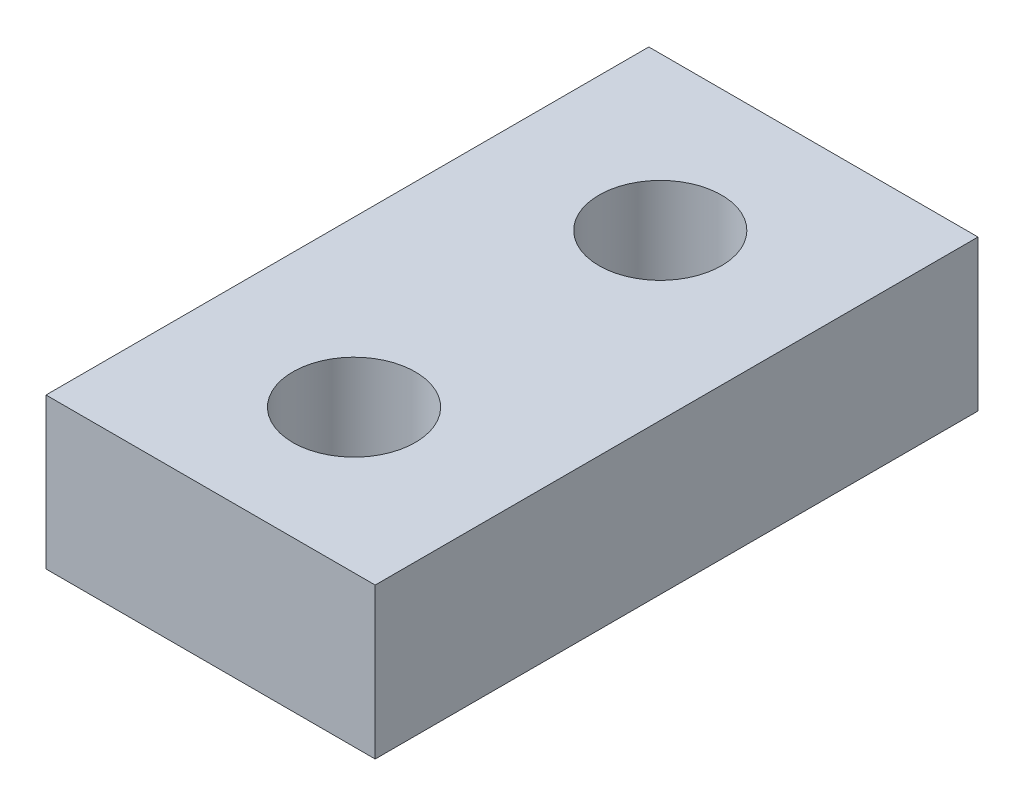
SolidWorks part; units mm, degrees
ref_plane "Front Plane" through (0, 0, 0) normal (0, 0, 1) x (1, 0, 0)
ref_plane "Top Plane" through (0, 0, 0) normal (0, 1, 0) x (1, 0, 0)
ref_plane "Right Plane" through (0, 0, 0) normal (1, 0, 0) x (0, 0, -1)
sketch "Sketch1" plane through (0, 0, 0) normal (0, 1, 0) x (1, 0, 0)
  line L1 (0, 0) -> (10.922, 0)
  line L2 (0, 0) -> (0, 20)
  line L3 (0, 20) -> (10.922, 20)
  line L4 (10.922, 0) -> (10.922, 20)
  circle A0 centre (5.461, 14.92) radius 2.032
  circle A1 centre (5.461, 4.76) radius 2.032
  point P9 (5.461, 20)
  dimension "D2" = 4.064
  dimension "D1" = 10.922
  dimension "D3" = 20
  dimension "D4" = 10.16
  dimension "D5" = 5.08
extrude "Boss-Extrude1" add sketch "Sketch1" along normal blind 5
